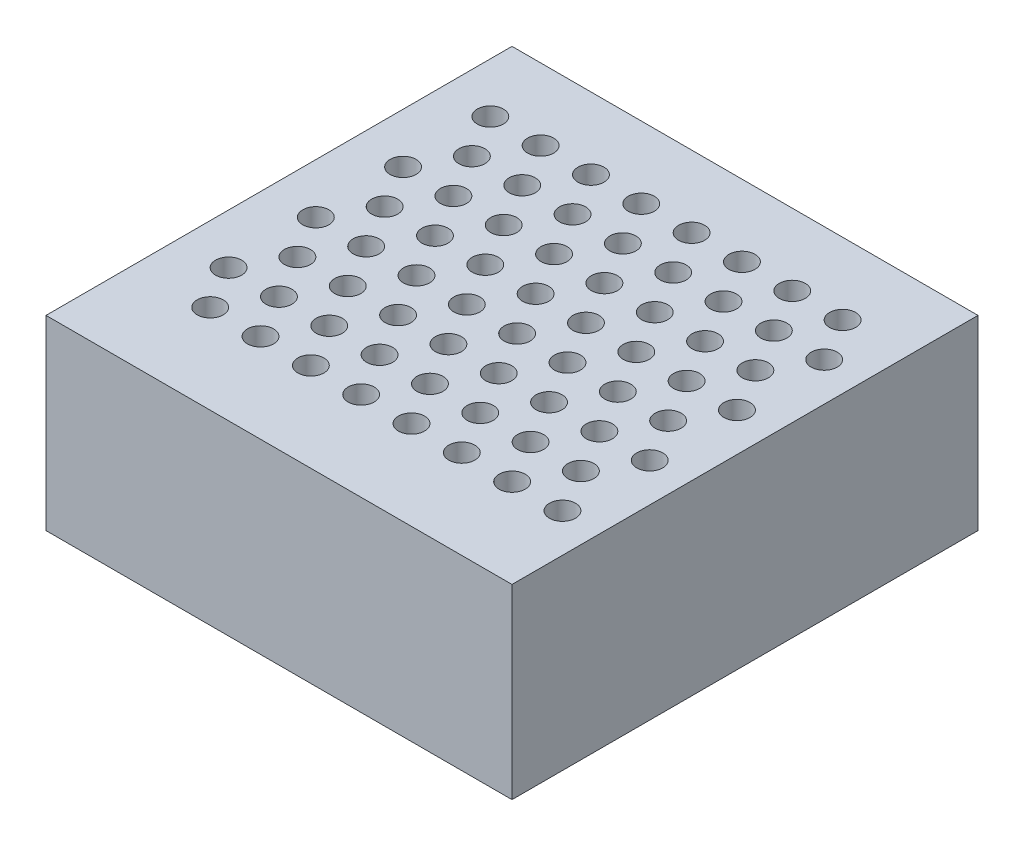
SolidWorks part; units mm, degrees
ref_plane "Front Plane" through (0, 0, 0) normal (0, 0, 1) x (1, 0, 0)
ref_plane "Top Plane" through (0, 0, 0) normal (0, 1, 0) x (1, 0, 0)
ref_plane "Right Plane" through (0, 0, 0) normal (1, 0, 0) x (0, 0, -1)
sketch "Sketch1" plane through (0, 0, 0) normal (0, 1, 0) x (1, 0, 0)
  line L1 (-41.8164, 24.4314) -> (-36.8164, 24.4314)
  line L2 (-41.8164, 24.4314) -> (-41.8164, 19.4314)
  line L3 (-41.8164, 19.4314) -> (-36.8164, 19.4314)
  line L4 (-36.8164, 24.4314) -> (-36.8164, 19.4314)
  dimension "D1" = 5
  dimension "D2" = 5
sketch "Sketch2" plane through (0, 0, 0) normal (0, 1, 0) x (1, 0, 0)
  circle A0 centre (-41.2803, 23.6626) radius 0.14
  circle A1 centre (-40.7403, 23.6626) radius 0.14
  circle A2 centre (-40.2003, 23.6626) radius 0.14
  circle A3 centre (-39.6603, 23.6626) radius 0.14
  circle A4 centre (-39.1203, 23.6626) radius 0.14
  circle A5 centre (-38.5803, 23.6626) radius 0.14
  circle A6 centre (-38.0403, 23.6626) radius 0.14
  circle A7 centre (-37.5003, 23.6626) radius 0.14
  circle A8 centre (-37.5003, 22.7266) radius 0.14
  circle A9 centre (-37.5003, 21.7906) radius 0.14
  circle A10 centre (-41.0103, 23.1949) radius 0.14
  circle A11 centre (-40.4703, 23.1949) radius 0.14
  circle A12 centre (-39.9303, 23.1949) radius 0.14
  circle A13 centre (-39.3903, 23.1949) radius 0.14
  circle A14 centre (-38.8503, 23.1949) radius 0.14
  circle A15 centre (-38.3103, 23.1949) radius 0.14
  circle A16 centre (-37.5003, 20.8546) radius 0.14
  circle A17 centre (-37.7703, 23.1949) radius 0.14
  circle A18 centre (-37.7703, 22.2589) radius 0.14
  circle A19 centre (-41.2803, 22.7266) radius 0.14
  circle A20 centre (-40.7403, 22.7266) radius 0.14
  circle A21 centre (-40.2003, 22.7266) radius 0.14
  circle A22 centre (-39.6603, 22.7266) radius 0.14
  circle A23 centre (-39.1203, 22.7266) radius 0.14
  circle A24 centre (-38.5803, 22.7266) radius 0.14
  circle A25 centre (-38.0403, 22.7266) radius 0.14
  circle A26 centre (-37.7703, 21.3229) radius 0.14
  circle A27 centre (-41.0103, 20.3869) radius 0.14
  circle A28 centre (-40.4703, 20.3869) radius 0.14
  circle A29 centre (-41.2803, 21.7906) radius 0.14
  circle A30 centre (-40.7403, 21.7906) radius 0.14
  circle A31 centre (-40.2003, 21.7906) radius 0.14
  circle A32 centre (-39.6603, 21.7906) radius 0.14
  circle A33 centre (-39.1203, 21.7906) radius 0.14
  circle A34 centre (-38.5803, 21.7906) radius 0.14
  circle A35 centre (-38.0403, 21.7906) radius 0.14
  circle A36 centre (-39.9303, 20.3869) radius 0.14
  circle A37 centre (-39.3903, 20.3869) radius 0.14
  circle A38 centre (-38.8503, 20.3869) radius 0.14
  circle A39 centre (-41.2803, 20.8546) radius 0.14
  circle A40 centre (-40.7403, 20.8546) radius 0.14
  circle A41 centre (-40.2003, 20.8546) radius 0.14
  circle A42 centre (-39.6603, 20.8546) radius 0.14
  circle A43 centre (-39.1203, 20.8546) radius 0.14
  circle A44 centre (-38.5803, 20.8546) radius 0.14
  circle A45 centre (-38.0403, 20.8546) radius 0.14
  circle A46 centre (-38.3103, 20.3869) radius 0.14
  circle A47 centre (-37.7703, 20.3869) radius 0.14
  circle A48 centre (-37.2303, 23.1949) radius 0.14
  circle A49 centre (-41.0103, 22.2589) radius 0.14
  circle A50 centre (-40.4703, 22.2589) radius 0.14
  circle A51 centre (-39.9303, 22.2589) radius 0.14
  circle A52 centre (-39.3903, 22.2589) radius 0.14
  circle A53 centre (-38.8503, 22.2589) radius 0.14
  circle A54 centre (-38.3103, 22.2589) radius 0.14
  circle A55 centre (-37.2303, 22.2589) radius 0.14
  circle A56 centre (-37.2303, 21.3229) radius 0.14
  circle A57 centre (-37.2303, 20.3869) radius 0.14
  circle A58 centre (-41.0103, 21.3229) radius 0.14
  circle A59 centre (-40.4703, 21.3229) radius 0.14
  circle A60 centre (-39.9303, 21.3229) radius 0.14
  circle A61 centre (-39.3903, 21.3229) radius 0.14
  circle A62 centre (-38.8503, 21.3229) radius 0.14
  circle A63 centre (-38.3103, 21.3229) radius 0.14
  dimension "D1" = 8
  dimension "D2" = 0.54
  dimension "D3" = 0.54
  dimension "D6" = 0.5406
  dimension "D4" = 8
  dimension "D5" = 4
  dimension "D7" = 4
extrude "Boss-Extrude1" add sketch "Sketch1" along normal blind 2
extrude "Cut-Extrude1" cut sketch "Sketch2" along normal blind 2
